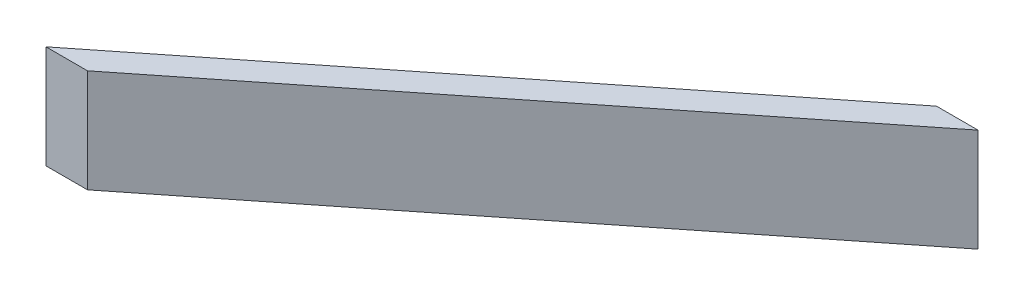
SolidWorks part; units mm, degrees
material "1.4301 (X5CrNi18-10)"
ref_plane "Ebene vorne" through (0, 0, 0) normal (0, 0, 1) x (1, 0, 0)
ref_plane "Ebene oben" through (0, 0, 0) normal (0, 1, 0) x (1, 0, 0)
ref_plane "Ebene rechts" through (0, 0, 0) normal (1, 0, 0) x (0, 0, -1)
sketch "Skizze2" plane through (0, 0, 0) normal (0, 1, 0) x (1, 0, 0)
  line L0 (-50, -76.3959) -> (46.3259, 0)
  line L1 (36.3259, 0) -> (61.3259, 0) construction
  line L2 (46.3259, 0) -> (54.3724, 0)
  line L3 (54.3724, 0) -> (-41.9536, -76.3959)
  line L4 (-50, -76.3959) -> (-41.9536, -76.3959)
  line L5 (36.3259, 5) -> (36.3259, 0) construction
  dimension "D1" = 5
  dimension "D2" = 10
extrude "Aufsatz-Linear austragen1" add sketch "Skizze2" along normal mid plane 20
